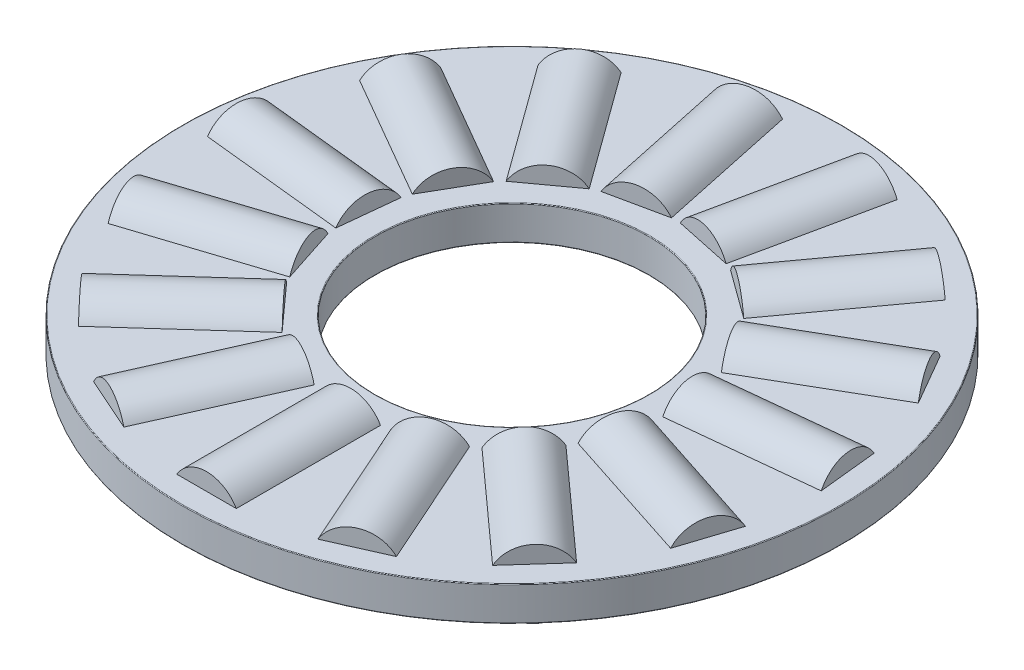
SolidWorks part; units mm, degrees
ref_plane "Front Plane" through (0, 0, 0) normal (0, 0, 1) x (1, 0, 0)
ref_plane "Top Plane" through (0, 0, 0) normal (0, 1, 0) x (1, 0, 0)
ref_plane "Right Plane" through (0, 0, 0) normal (1, 0, 0) x (0, 0, -1)
sketch "Sketch1" plane through (0, 0, 0) normal (1, 0, 0) x (0, 0, -1)
  line L0 (-9.525, 0) -> (9.525, 0) construction
  line L1 (0, -0.9922) -> (0, 0.9922) construction
  line L2 (-9.525, 0.4961) -> (-3.9624, 0.4961)
  line L3 (-9.525, 0.4961) -> (-9.525, -0.4961)
  line L4 (-9.525, -0.4961) -> (-3.9624, -0.4961)
  line L5 (-3.9624, 0.4961) -> (-3.9624, -0.4961)
  line L7 (-6.7437, 0.9922) -> (-6.7437, 0.4961) construction
  line L8 (-8.8273, 0.9922) -> (-4.6601, 0.9922) construction
  line L9 (-8.8273, 0.9922) -> (-8.8273, -0.9922) construction
  line L10 (-8.8273, -0.9922) -> (-4.6601, -0.9922) construction
  line L11 (-4.6601, 0.9922) -> (-4.6601, -0.9922) construction
  point P16 (-8.8273, 0)
  dimension "OD" = 19.05
  dimension "Shaft Dia" = 7.9248
  dimension "Th" = 1.9844
  dimension "D2" = 0.9922
  dimension "D1" = 4.1672
  dimension "D3" = 5.5626
revolve "Revolve1" add sketch "Sketch1" angle 360 about L1
sketch "Sketch3" plane through (0, 0, 0) normal (1, 0, 0) x (0, 0, -1)
  line L0 (-8.8273, 0.9922) -> (-8.8273, -0.9922) construction
  line L1 (-8.8273, 0) -> (-4.6601, 0)
  line L2 (-8.8273, 0) -> (-8.8273, 0.9922)
  line L3 (-8.8273, 0.9922) -> (-4.6601, 0.9922)
  line L4 (-4.6601, 0) -> (-4.6601, 0.9922)
revolve "Cut-Revolve1" cut sketch "Sketch3" angle 360 about L1
sketch "Sketch2" plane through (0, 0, 0) normal (1, 0, 0) x (0, 0, -1)
  line L1 (-8.8273, 0) -> (-4.6601, 0)
  line L2 (-8.8273, 0) -> (-8.8273, 0.9922)
  line L3 (-8.8273, 0.9922) -> (-4.6601, 0.9922)
  line L4 (-4.6601, 0) -> (-4.6601, 0.9922)
revolve "Revolve2" add sketch "Sketch2" angle 360 about L1
ref_axis "Axis1" through (0, 0.9922, 0) along (0, -1, 0)
pattern_circular "CirPattern1" count 15 every 24 about axis through (0, 0.9922, 0) along (0, -1, 0) of bodies 187 411
pattern_circular "CirPattern2" count 15 every 24 about axis through (0, 0, 0) along (0, 1, 0) of "Cut-Revolve1"
sketch "Sketch4" plane through (0, 0, 0) normal (1, 0, 0) x (0, 0, -1)
  line L0 (-9.525, 0.4961) -> (-9.525, -0.4961) construction
  line L1 (-11.9062, 9.1091) -> (-6.35, 9.1091)
  line L2 (-11.9062, 9.1091) -> (-11.9062, 9.9219)
  line L3 (-11.9062, 9.9219) -> (-6.35, 9.9219)
  line L4 (-6.35, 9.1091) -> (-6.35, 9.9219)
  line L5 (-11.9062, -9.9219) -> (-3.9624, -9.9219)
  line L6 (-11.9062, -9.9219) -> (-11.9062, -9.1091)
  line L7 (-11.9062, -9.1091) -> (-3.9624, -9.1091)
  line L8 (-3.9624, -9.9219) -> (-3.9624, -9.1091)
  line L10 (-3.9624, 0.4961) -> (-3.9624, -0.4961) construction
  line L11 (0, 0) -> (-9.525, 0) construction
  line L12 (-9.525, 0) -> (9.525, 0) construction
  line L13 (0, -0.9922) -> (0, 0.9922) construction
  dimension "Ht" = 19.8438
  dimension "Washer Th" = 0.8128
  dimension "Washer ID" = 12.7
  dimension "Washer OD" = 23.8125
fillet "Fillet2" radius 0.0198 4 edges at (0, -0.4961, -3.9624) (0, 0.4961, -3.9624) (0, -0.4961, -9.525) (0, 0.4961, -9.525)
equation "\"D2@Sketch1\"= \"Th@Sketch1\" * .5"
equation "\"Rollers@CirPattern1\"= \"OD@Sketch1\" * 20"
equation "\"Angle@CirPattern1\" = 360/\"Rollers@CirPattern1\""
equation "\"D1@CirPattern2\" = \"Rollers@CirPattern1\""
equation "\"D2@CirPattern2\" = \"Angle@CirPattern1\""
equation "\"Ht@Sketch4\" = \"Th@Sketch1\"*10"
